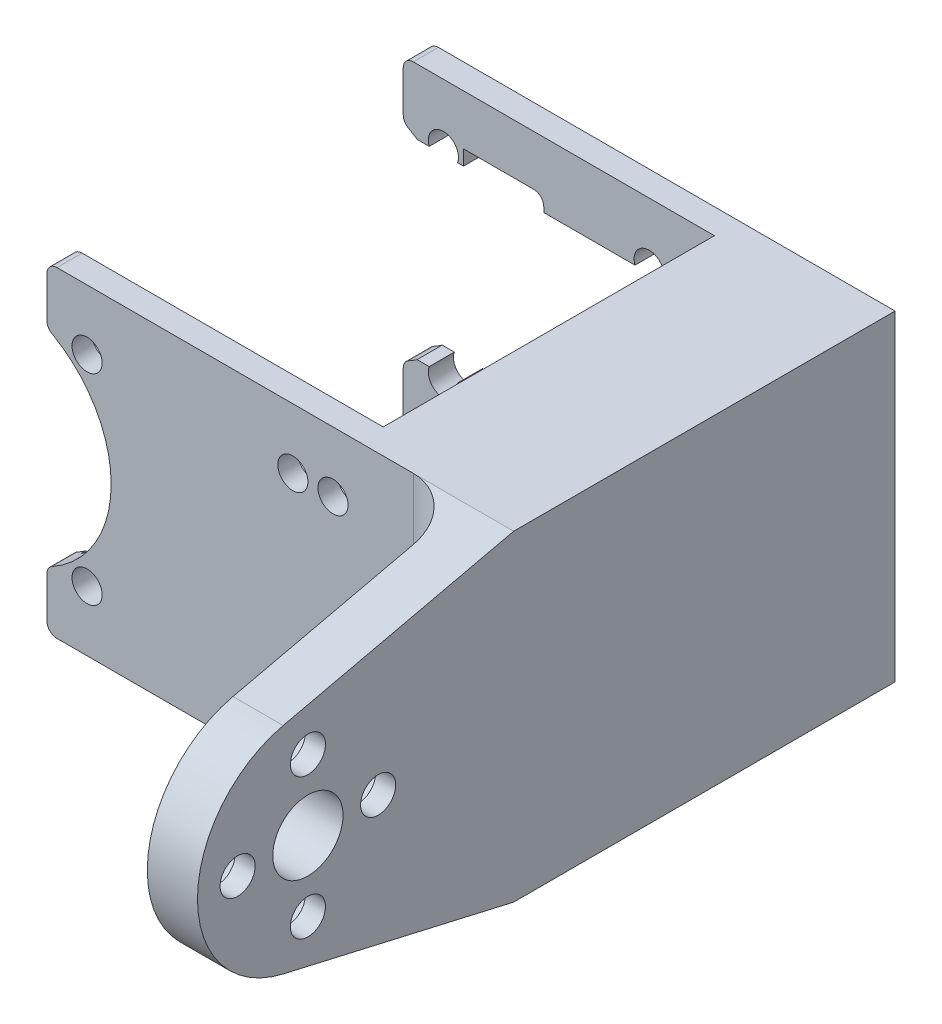
SolidWorks part; units mm, degrees
ref_plane "Спереди" through (0, 0, 0) normal (0, 0, 1) x (1, 0, 0)
ref_plane "Сверху" through (0, 0, 0) normal (0, 1, 0) x (1, 0, 0)
ref_plane "Справа" through (0, 0, 0) normal (1, 0, 0) x (0, 0, -1)
other "Configuration Table"
sketch "Эскиз1" plane through (0, 0, 0) normal (0, 0, 1) x (1, 0, 0)
  line L1 (10.25, -10) -> (-10.25, -10) construction
  line L2 (10.25, -10) -> (10.25, 10) construction
  line L3 (10.25, 10) -> (-10.25, 10) construction
  line L4 (-10.25, -10) -> (-10.25, 10) construction
  line L5 (10.25, -10) -> (-10.25, 10) construction
  line L6 (10.25, 10) -> (-10.25, -10) construction
  line L7 (10.25, 10) -> (14.25, 10) construction
  line L8 (10.25, 10) -> (10.25, -10) construction
  line L9 (10.25, -10) -> (14.25, -10) construction
  line L10 (14.25, 10) -> (14.25, -10) construction
  line L11 (-14.25, 16) -> (19.25, 16)
  line L12 (-14.25, 16) -> (-14.25, -16)
  line L13 (-14.25, -16) -> (19.25, -16)
  line L14 (19.25, 16) -> (19.25, -16)
  circle A0 centre (-10.25, 10) radius 1.5
  circle A1 centre (10.25, 10) radius 1.5
  circle A2 centre (14.25, 10) radius 1.5
  circle A3 centre (14.25, -10) radius 1.5
  circle A4 centre (-10.25, -10) radius 1.5
  circle A5 centre (10.25, -10) radius 1.5
  point P0 (0, 0)
  dimension "D4" = 3
  dimension "D1" = 4
  dimension "D2" = 20.5
  dimension "D3" = 20
  dimension "D5" = 4
  dimension "D6" = 6
  dimension "D7" = 6
  dimension "D8" = 5
extrude "Бобышка-Вытянуть1" add sketch "Эскиз1" against normal blind 38 contours L14 L11 L12 L13 A5 A4 A3 A2 A1 A0
sketch "Эскиз2" plane through (-14.25, 0, 0) normal (-1, 0, 0) x (0, 0, 1)
  line L0 (-38, 16) -> (0, 16) construction
  line L1 (-35.5, 16) -> (-2.5, 16)
  line L2 (-35.5, 16) -> (-35.5, -16)
  line L3 (-35.5, -16) -> (-2.5, -16)
  line L4 (-2.5, 16) -> (-2.5, -16)
  line L5 (-38, -16) -> (0, -16) construction
  line L6 (0, 16) -> (0, -16) construction
  line L7 (-38, 16) -> (-38, -16) construction
  dimension "D1" = 2.5
  dimension "D2" = 2.5
extrude "Вырез-Вытянуть1" cut sketch "Эскиз2" against normal blind 31
sketch "Эскиз4" plane through (0, 0, -38) normal (0, 0, -1) x (-1, 0, 0)
  line L0 (10.25, 10) -> (10.25, -10) construction
  line L1 (10.25, 0) -> (19.35, 0) construction
  circle A0 centre (19.35, 0) radius 11.5
  dimension "D2" = 23
  dimension "D1" = 9.1
extrude "Вырез-Вытянуть2" cut sketch "Эскиз4" against normal through all
sketch "Эскиз5" plane through (0, 0, -35.5) normal (0, 0, 1) x (1, 0, 0)
  line L0 (-14.25, 16) -> (-14.25, 10.3073) construction
  line L1 (-14.25, 9.5) -> (16.75, 9.5)
  line L2 (-14.25, 9.5) -> (-14.25, -9.5)
  line L3 (-14.25, -9.5) -> (16.75, -9.5)
  line L4 (16.75, 9.5) -> (16.75, -9.5)
  line L5 (-14.25, 0) -> (0, 0) construction
  dimension "D1" = 19
  dimension "D2" = 31
extrude "Вырез-Вытянуть3" cut sketch "Эскиз5" against normal blind 11.5 and the other way blind 33.5
sketch "Эскиз8" plane through (19.25, 0, 0) normal (1, 0, 0) x (0, 0, -1)
  line L0 (38, 16) -> (38, -16) construction
  line L1 (0, 16) -> (38, 16)
  line L2 (0, 16) -> (0, -16)
  line L3 (0, -16) -> (38, -16)
  line L4 (38, 16) -> (38, -16)
  line L5 (38, -16) -> (0, -16) construction
extrude "Бобышка-Вытянуть3" add sketch "Эскиз8" along normal blind 4
sketch "Эскиз10" plane through (23.25, 0, 0) normal (1, 0, 0) x (0, 0, -1)
  line L0 (-20.5, 0) -> (38, 0) construction
  line L1 (38, -16) -> (38, 16) construction
  line L2 (0, 16) -> (-22.9646, 10.7203)
  line L4 (0, -16) -> (-22.9646, -10.7203)
  line L6 (0, 16) -> (38, 16)
  line L8 (0, -16) -> (38, -16)
  line L9 (38, 16) -> (38, -16)
  circle A0 centre (-20.5, 0) radius 11
  dimension "D2" = 22
  dimension "D1" = 58.5
extrude "Бобышка-Вытянуть4" add sketch "Эскиз10" along normal blind 9
sketch "Эскиз11" plane through (0, 0, -38) normal (0, 0, -1) x (-1, 0, 0)
  line L0 (19.35, 0) -> (4.25, 0) construction
  line L2 (0.25, 11) -> (8.25, 11)
  line L3 (0.25, 11) -> (0.25, -11)
  line L4 (0.25, -11) -> (8.25, -11)
  line L5 (8.25, 11) -> (8.25, -11)
  line L6 (0.25, 11) -> (8.25, -11) construction
  line L7 (0.25, -11) -> (8.25, 11) construction
  line L8 (8.25, 7) -> (10.2259, 7)
  line L9 (8.25, 7) -> (8.25, -7)
  line L10 (8.25, -7) -> (10.2259, -7)
  line L11 (10.2259, 7) -> (10.2259, -7)
  circle A0 centre (19.35, 0) radius 11.5 construction
  arc A1 (14.25, 10.3073) -> (12.8693, 9.5) centre (19.35, 0) ccw construction
  point P15 (8.25, 0)
  line M31 (-8.8358, 9.5) -> (8.8358, 9.5)
  line M35 (8.8358, -9.5) -> (-8.8358, -9.5)
  dimension "D1" = 8
  dimension "D2" = 22
  dimension "D3" = 4
  dimension "D4" = 15.1
extrude "Вырез-Вытянуть4" cut sketch "Эскиз11" against normal blind 10 contours L5 L2 L3 M31 | L5 L3 L4 M35
fillet "Скругление3" radius 1 11 edges at (-14.25, -16, -1.25) (-14.25, -10.3073, -1.25) (-14.25, 10.3073, -1.25) (-14.25, 16, -1.25) (-14.25, -16, -36.75) (-0.25, -11, -36.75) (-0.25, 11, -36.75) (-8.25, -11, -36.75) (-14.25, 16, -36.75) (-14.25, 10.3073, -36.75) (-14.25, -10.3073, -36.75)
sketch "Эскиз12" plane through (32.25, 0, 0) normal (1, 0, 0) x (0, 0, -1)
  circle A0 centre (-20.5, 0) radius 7 construction
  arc A1 (-22.9646, 10.7203) -> (-22.9646, -10.7203) centre (-20.5, 0) ccw construction
  circle A2 centre (-27.5, 0) radius 1.75
  circle A3 centre (-20.5, 7) radius 1.75
  circle A4 centre (-13.5, 0) radius 1.75
  circle A5 centre (-20.5, -7) radius 1.75
  dimension "D1" = 14
  dimension "D2" = 3.5
extrude "Вырез-Вытянуть5" cut sketch "Эскиз12" against normal through all
sketch "Эскиз13" plane through (23.25, 0, 0) normal (-1, 0, 0) x (0, 0, 1)
  circle A0 centre (20.5, 0) radius 3.5
  arc A1 (22.9646, -10.7203) -> (22.9646, 10.7203) centre (20.5, 0) ccw construction
  dimension "D1" = 7
extrude "Вырез-Вытянуть6" cut sketch "Эскиз13" against normal blind 10
sketch "Эскиз15" plane through (23.25, 0, 0) normal (-1, 0, 0) x (0, 0, 1)
  line L1 (0, 16) -> (31.5, 16)
  line L2 (0, 16) -> (0, -16)
  line L3 (0, -16) -> (31.5, -16)
  line L4 (31.5, 16) -> (31.5, -16)
  arc A0 (22.9646, -10.7203) -> (22.9646, 10.7203) centre (20.5, 0) ccw construction
extrude "Вырез-Вытянуть7" cut sketch "Эскиз15" against normal blind 4
sketch "Эскиз16" plane through (27.25, 0, 0) normal (-1, 0, 0) x (0, 0, 1)
  circle A0 centre (20.5, 7) radius 3
  circle A1 centre (27.5, 0) radius 3
  circle A2 centre (20.5, -7) radius 3
  circle A3 centre (13.5, 0) radius 3
  dimension "D1" = 6
extrude "Вырез-Вытянуть8" cut sketch "Эскиз16" against normal blind 3
fillet "Скругление4" radius 5 1 edges at (27.25, 0, 0)
